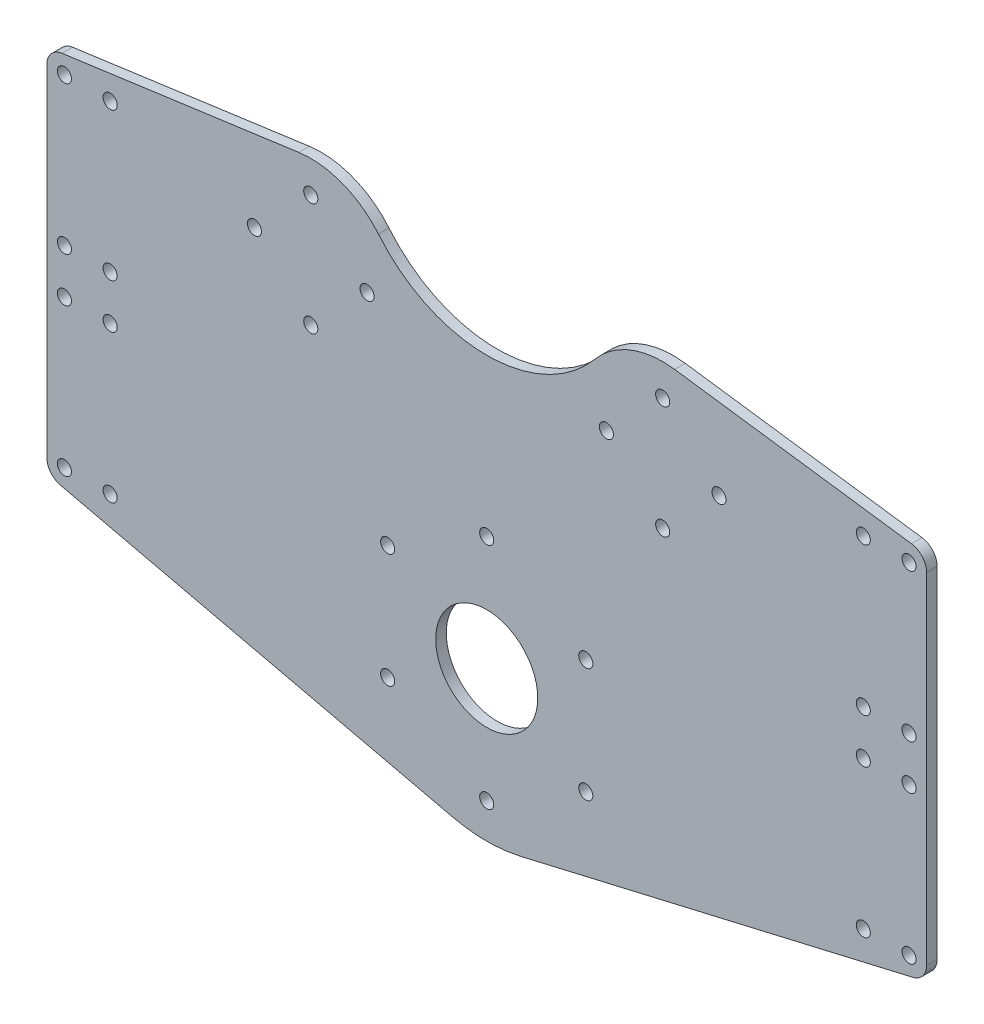
SolidWorks part; units mm, degrees
material "1060 Alloy"
ref_plane "Front Plane" through (0, 0, 0) normal (0, 0, 1) x (1, 0, 0)
ref_plane "Top Plane" through (0, 0, 0) normal (0, 1, 0) x (1, 0, 0)
ref_plane "Right Plane" through (0, 0, 0) normal (1, 0, 0) x (0, 0, -1)
sketch "Sketch1" plane through (0, 0, 0) normal (0, 0, 1) x (1, 0, 0)
  line L1 (-125, 10.5588) -> (-125, -86.1125)
  line L2 (-121.134, -90.9822) -> (-9.6391, -116.9462)
  line L3 (-120.6814, 15.5122) -> (-53.407, 24.7668)
  line L4 (125, 10.5588) -> (125, -86.1125)
  line L5 (121.134, -90.9822) -> (9.6391, -116.9462)
  line L6 (120.6814, 15.5122) -> (53.407, 24.7668)
  line L7 (-50, 0) -> (50, 0) construction
  line L8 (0, -75.5537) -> (0, 0) construction
  arc A0 (-30.7692, 15.9743) -> (-53.407, 24.7668) centre (-50, 0) ccw
  arc A1 (53.407, 24.7668) -> (30.7692, 15.9743) centre (50, 0) ccw
  arc A2 (-9.6391, -116.9462) -> (9.6391, -116.9462) centre (0, -75.5537) ccw
  circle A13 centre (0, -75.5537) radius 14.5
  arc A14 (-30.7692, 15.9743) -> (30.7692, 15.9743) centre (0, 41.5331) ccw
  arc A15 (125, 10.5588) -> (120.6814, 15.5122) centre (120, 10.5588) ccw
  arc A16 (125, -86.1125) -> (121.134, -90.9822) centre (120, -86.1125) cw
  arc A17 (-125, -86.1125) -> (-121.134, -90.9822) centre (-120, -86.1125) ccw
  arc A18 (-125, 10.5588) -> (-120.6814, 15.5122) centre (-120, 10.5588) cw
  point P18 (0, -37.7768)
  point P19 (125, -37.7768)
  point P29 (125, 14.9181)
  point P33 (125, -90.0819)
  point P36 (-125, -90.0819)
  point P39 (-125, 14.9181)
  dimension "D3" = 50
  dimension "D4" = 50
  dimension "D5" = 85
  dimension "D6" = 120
  dimension "D8" = 50
  dimension "D11" = 29
  dimension "D9" = 80
  dimension "D13" = 5
  dimension "D1" = 100
  dimension "D2" = 120
  dimension "D7" = 105
  dimension "D12" = 90.6
extrude "Boss-Extrude1" add sketch "Sketch1" along normal blind 3
hole_wizard "M4 Clearance Hole1" positions "Sketch5" profile "Sketch3" hole size "M4" standard "ISO"
sketch "Sketch5" plane through (0, 0, 3) normal (0, 0, 1) x (1, 0, 0)
  line L0 (-50, 0) -> (50, 0) construction
  circle A0 centre (-50, 0) radius 16 construction
  circle A1 centre (50, 0) radius 16 construction
  point P0 (-66, 0)
  point P16 (0, 0)
  point P17 (-34, 0)
  point P19 (-50, 16)
  point P21 (-50, -16)
  point P23 (34, 0)
  point P25 (50, 16)
  point P27 (66, 0)
  point P29 (50, -16)
  dimension "D1" = 32
  dimension "D2" = 100
sketch "Sketch3" plane through (-66, 0, 3) normal (1, 0, 0) x (0, -1, 0)
  line L0 (0, 0) -> (0, 11.2017)
  line L1 (0, 11.2017) -> (2, 10)
  line L2 (2, 10) -> (2, 0)
  line L5 (2, 0) -> (0, 0)
  line L10 (0, 11.2017) -> (-2, 10) construction
  line L11 (0, -6.35) -> (0, 107.95) construction
  dimension "Hole Dia." = 4
  dimension "Hole Depth" = 10
  dimension "Drill Angle" = 118
hole_wizard "M4 Clearance Hole2" positions "Sketch7" profile "Sketch8" hole size "M4" standard "ISO"
sketch "Sketch7" plane through (0, 0, 3) normal (0, 0, 1) x (1, 0, 0)
  circle A0 centre (0, -75.5537) radius 32.5 construction
  point P0 (0, -108.0537)
  dimension "D1" = 65
sketch "Sketch8" plane through (0, -108.0537, 3) normal (1, 0, 0) x (0, -1, 0)
  line L0 (0, 0) -> (0, 11.2017)
  line L1 (0, 11.2017) -> (2, 10)
  line L2 (2, 10) -> (2, 0)
  line L5 (2, 0) -> (0, 0)
  line L10 (0, 11.2017) -> (-2, 10) construction
  line L11 (0, -6.35) -> (0, 107.95) construction
  dimension "Hole Dia." = 4
  dimension "Hole Depth" = 10
  dimension "Drill Angle" = 118
pattern_circular "CirPattern1" count 6 over 360 about axis through (0, -75.5537, 0) along (0, 0, 1) of "M4 Clearance Hole2"
hole_wizard "M4 Clearance Hole3" positions "Sketch9" profile "Sketch10" hole size "M4" standard "ISO" end condition through all
sketch "Sketch9" plane through (0, 0, 3) normal (0, 0, 1) x (1, 0, 0)
  line L1 (-120, 10.5588) -> (-107, 10.5588) construction
  line L2 (-120, 10.5588) -> (-120, -31.4412) construction
  line L3 (-120, -31.4412) -> (-107, -31.4412) construction
  line L4 (-107, 10.5588) -> (-107, -31.4412) construction
  line L6 (-120, -86.1125) -> (-107, -86.1125) construction
  line L7 (-120, -86.1125) -> (-120, -44.1125) construction
  line L8 (-120, -44.1125) -> (-107, -44.1125) construction
  line L9 (-107, -86.1125) -> (-107, -44.1125) construction
  line L11 (120, 10.5588) -> (107, 10.5588) construction
  line L12 (120, 10.5588) -> (120, -31.4412) construction
  line L13 (120, -31.4412) -> (107, -31.4412) construction
  line L14 (107, 10.5588) -> (107, -31.4412) construction
  line L16 (120, -86.1125) -> (107, -86.1125) construction
  line L17 (120, -86.1125) -> (120, -44.1125) construction
  line L18 (120, -44.1125) -> (107, -44.1125) construction
  line L19 (107, -86.1125) -> (107, -44.1125) construction
  arc A0 (-120.6814, 15.5122) -> (-125, 10.5588) centre (-120, 10.5588) ccw construction
  arc A1 (-125, -86.1125) -> (-121.134, -90.9822) centre (-120, -86.1125) ccw construction
  arc A2 (125, 10.5588) -> (120.6814, 15.5122) centre (120, 10.5588) ccw construction
  point P0 (-120, 10.5588)
  point P2 (-107, 10.5588)
  point P4 (-120, -31.4412)
  point P6 (-107, -31.4412)
  point P119 (-120, -86.1125)
  point P120 (-107, -44.1125)
  point P191 (-120, -44.1125)
  point P192 (-107, -86.1125)
  point P208 (120, 10.5588)
  point P209 (107, -31.4412)
  point P292 (120, -31.4412)
  point P293 (107, 10.5588)
  point P295 (120, -86.1125)
  point P296 (107, -44.1125)
  point P411 (120, -44.1125)
  point P412 (107, -86.1125)
  dimension "D1" = 42
  dimension "D2" = 13
  dimension "D3" = 12.6713
sketch "Sketch10" plane through (-120, 10.5588, 3) normal (1, 0, 0) x (0, -1, 0)
  line L0 (0, 0) -> (0, 3)
  line L1 (0, 3) -> (2, 3)
  line L2 (2, 3) -> (2, 0)
  line L5 (2, 0) -> (0, 0)
  line L11 (0, -6.35) -> (0, 107.95) construction
  dimension "Thru Hole Dia." = 4
  dimension "Thru Hole Depth" = 3
